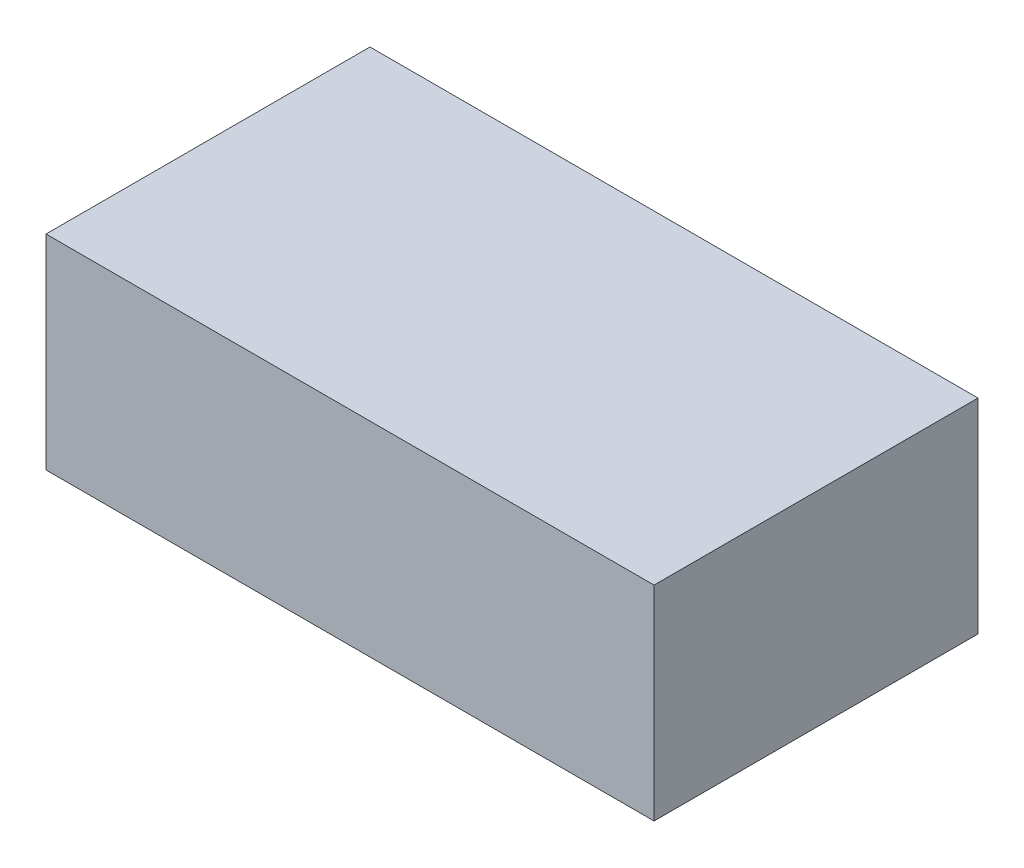
SolidWorks part; units mm, degrees
ref_plane "前基準面" through (0, 0, 0) normal (0, 0, 1) x (1, 0, 0)
ref_plane "上基準面" through (0, 0, 0) normal (0, 1, 0) x (1, 0, 0)
ref_plane "右基準面" through (0, 0, 0) normal (1, 0, 0) x (0, 0, -1)
sketch "草圖1" plane through (0, 0, 0) normal (0, 1, 0) x (1, 0, 0)
  line L1 (-61, 32.5) -> (61, 32.5)
  line L2 (-61, 32.5) -> (-61, -32.5)
  line L3 (-61, -32.5) -> (61, -32.5)
  line L4 (61, 32.5) -> (61, -32.5)
  line L5 (-61, 32.5) -> (61, -32.5) construction
  line L6 (-61, -32.5) -> (61, 32.5) construction
  point P0 (0, 0)
extrude "填料-伸長1" add sketch "草圖1" along normal blind 41
